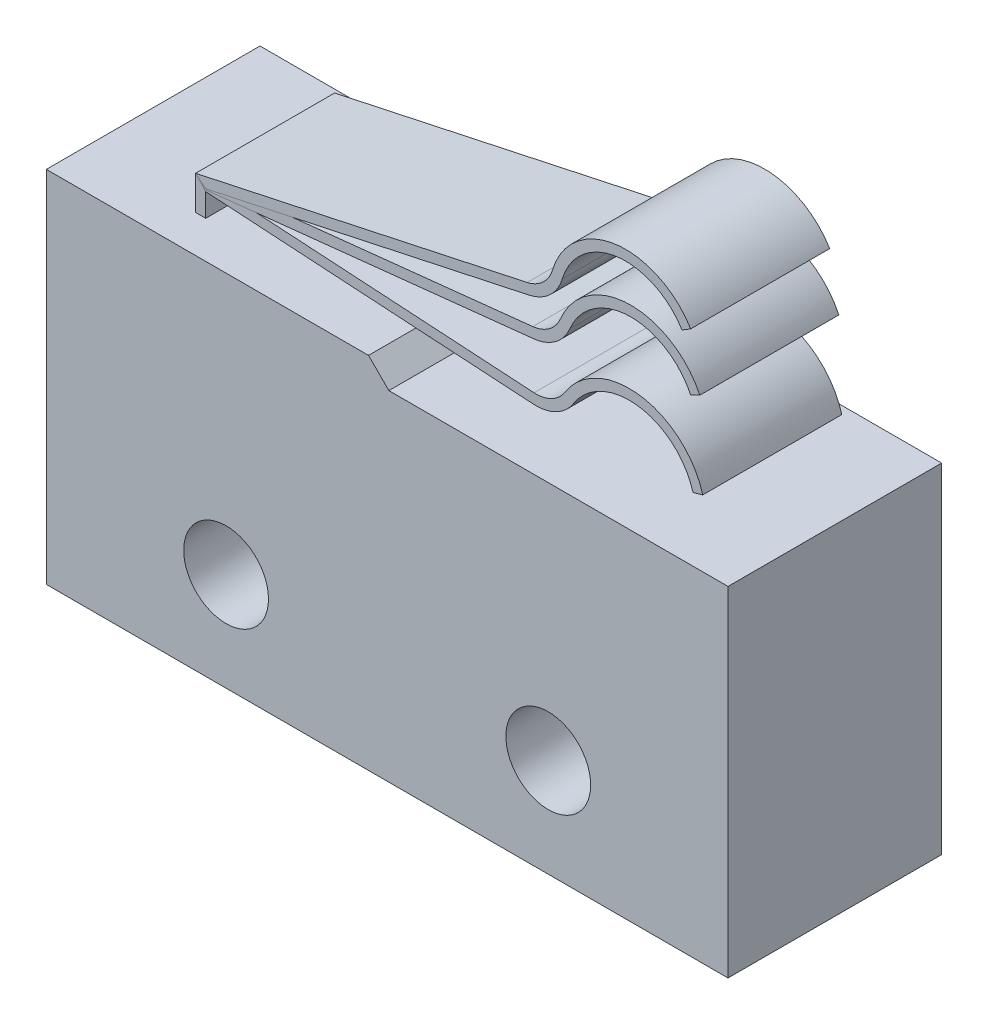
SolidWorks part; units mm, degrees
ref_plane "Front plane" through (0, 0, 0) normal (0, 0, 1) x (1, 0, 0)
ref_plane "Top plane" through (0, 0, 0) normal (0, 1, 0) x (1, 0, 0)
ref_plane "Right Plane" through (0, 0, 0) normal (1, 0, 0) x (0, 0, -1)
sketch "Sketch1" plane through (0, 0, 0) normal (0, 0, 1) x (1, 0, 0)
  line L0 (4.2, 7.7) -> (4.8, 7.1)
  line L1 (-5.3, 7.7) -> (4.2, 7.7)
  line L2 (-5.3, 7.7) -> (-5.3, -2.9)
  line L3 (-5.3, -2.9) -> (14.8, -2.9)
  line L4 (14.8, 7.1) -> (14.8, -2.9)
  line L5 (4.8, 7.1) -> (14.8, 7.1)
  line L6 (0, 0) -> (9.5, 0) construction
  circle A0 centre (0, 0) radius 1.25
  circle A1 centre (9.5, 0) radius 1.25
  point P8 (4.75, 0)
  point P9 (4.75, -2.9)
  dimension "D1" = 2.5
  dimension "D2" = 9.5
  dimension "D3" = 20.1
  dimension "D4" = 10
  dimension "D5" = 10.6
  dimension "D6" = 135
  dimension "D7" = 10
  dimension "D9" = 7.7
extrude "Boss-Extrude1" add sketch "Sketch1" along normal mid plane 6.3
sketch "Sketch2" plane through (0, 0, 0) normal (0, 0, 1) x (1, 0, 0)
  line L0 (-2, 7.7) -> (-2, 8.7)
  line L1 (4.2, 7.7) -> (-5.3, 7.7) construction
  line L2 (-2, 8.7) -> (7.777, 10.8)
  line L3 (-1.7, 7.7) -> (-1.7, 8.4576)
  line L4 (-1.7, 8.4576) -> (7.84, 10.5067)
  line L5 (12.3442, 11.8692) -> (12.6, 12.026)
  line L6 (-2, 7.7) -> (-1.7, 7.7)
  line L7 (-5.3, 7.7) -> (-5.3, -2.9) construction
  line L8 (14.8, -2.9) -> (14.8, 7.1) construction
  line L9 (14.8, 7.1) -> (4.8, 7.1) construction
  arc A0 (7.777, 10.8) -> (8.5254, 11.4923) centre (7.567, 11.7777) ccw
  arc A1 (8.5254, 11.4923) -> (12.6, 12.026) centre (10.6818, 10.85) cw
  arc A2 (7.84, 10.5067) -> (8.8129, 11.4066) centre (7.567, 11.7777) ccw
  arc A3 (8.8129, 11.4066) -> (12.3442, 11.8692) centre (10.6818, 10.85) cw
  point P25 (10.6818, 13.1)
  dimension "D4" = 1
  dimension "D5" = 2.25
  dimension "D2" = 1
  dimension "D3" = 10
  dimension "D6" = 3.3
  dimension "D7" = 2.2
  dimension "D8" = 3.7
  dimension "D9" = 6
  dimension "D1" = 0.3
extrude "Boss-Extrude2" add sketch "Sketch2" along normal mid plane 4.1 separate body
sketch "Sketch3" plane through (0, 0, 0) normal (0, 0, 1) x (1, 0, 0)
  line L0 (-2, 7.7) -> (-2, 8.7)
  line L1 (-2, 8.7) -> (7.944, 9.7567)
  line L2 (-1.7, 8.4302) -> (7.9757, 9.4584)
  line L3 (12.5985, 10.3381) -> (12.8694, 10.4671)
  line L4 (7.777, 10.8) -> (-2, 8.7) construction
  line L5 (7.777, 10.8) -> (8.5254, 11.4923) construction
  line L6 (8.7613, 10.3662) -> (7.944, 9.7567) construction
  line L7 (8.5254, 11.4923) -> (12.6, 12.026) construction
  line L8 (8.7613, 10.3662) -> (12.8694, 10.4671) construction
  line L9 (14.8, 7.1) -> (4.8, 7.1) construction
  line L10 (-1.7, 7.7) -> (-1.7, 8.4576) construction
  line L11 (-1.7, 7.7) -> (-1.7, 8.4302)
  line L12 (-2, 7.7) -> (-1.7, 7.7) construction
  line L13 (-2, 7.7) -> (-1.7, 7.7)
  line L15 (-1.9683, 8.4017) -> (7.9757, 9.4584) construction
  arc A0 (7.944, 9.7567) -> (8.7613, 10.3662) centre (7.8383, 10.7512) ccw
  arc A1 (8.7613, 10.3662) -> (12.8694, 10.4671) centre (10.8379, 9.5) cw
  arc A2 (7.9757, 9.4584) -> (9.0381, 10.2507) centre (7.8383, 10.7512) ccw
  arc A3 (9.0381, 10.2507) -> (12.5985, 10.3381) centre (10.8379, 9.5) cw
  arc A4 (7.777, 10.8) -> (8.5254, 11.4923) centre (7.567, 11.7777) ccw construction
  arc A5 (12.6, 12.026) -> (8.5254, 11.4923) centre (10.6818, 10.85) ccw construction
  point P30 (10.8379, 11.75)
  dimension "D2" = 4.65
  dimension "D1" = 0.3
extrude "Boss-Extrude3" add sketch "Sketch3" along normal mid plane 4.1 separate body
sketch "Sketch4" plane through (0, 0, 0) normal (0, 0, 1) x (1, 0, 0)
  line L0 (-2, 8.7) -> (-2, 7.7) construction
  line L1 (-2, 8.7) -> (-2, 7.7)
  line L2 (-2, 8.7) -> (7.9811, 8.0853)
  line L3 (7.9811, 8.0853) -> (8.8885, 8.55) construction
  line L4 (12.956, 7.9651) -> (8.8885, 8.55) construction
  line L5 (8.7613, 10.3662) -> (7.944, 9.7567) construction
  line L6 (8.7613, 10.3662) -> (12.8694, 10.4671) construction
  line L7 (-2, 8.7) -> (7.944, 9.7567) construction
  line L8 (14.8, 7.1) -> (4.8, 7.1) construction
  line L9 (-1.7, 8.381) -> (7.9626, 7.7859)
  line L10 (-1.7, 8.381) -> (-1.7, 7.7)
  line L11 (-2, 7.7) -> (-1.7, 7.7)
  line L12 (12.6674, 7.8831) -> (12.956, 7.9651)
  arc A0 (7.9811, 8.0853) -> (8.8885, 8.55) centre (8.0426, 9.0834) ccw
  arc A1 (8.8885, 8.55) -> (12.956, 7.9651) centre (10.7917, 7.35) cw
  arc A2 (12.8694, 10.4671) -> (8.7613, 10.3662) centre (10.8379, 9.5) ccw construction
  arc A3 (7.944, 9.7567) -> (8.7613, 10.3662) centre (7.8383, 10.7512) ccw construction
  arc A4 (9.1422, 8.39) -> (12.6674, 7.8831) centre (10.7917, 7.35) cw
  arc A5 (7.9626, 7.7859) -> (9.1422, 8.39) centre (8.0426, 9.0834) ccw
  point P19 (10.7917, 9.6)
  dimension "D1" = 2.5
  dimension "D2" = 0.3
extrude "Boss-Extrude4" add sketch "Sketch4" along normal mid plane 4.1 separate body
